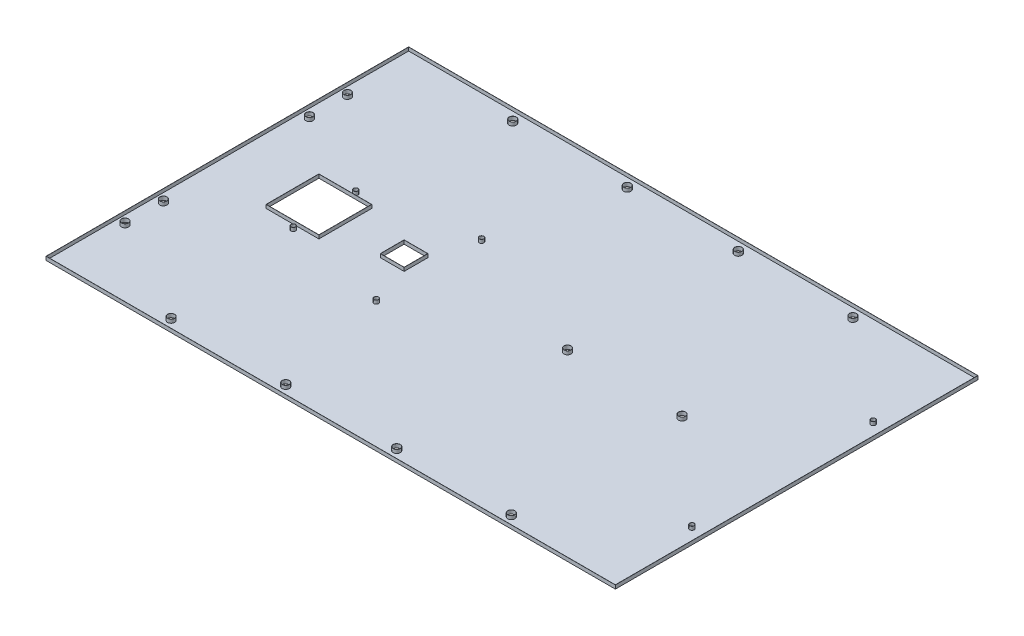
SolidWorks part; units mm, degrees
ref_plane "Front Plane" through (0, 0, 0) normal (0, 0, 1) x (1, 0, 0)
ref_plane "Top Plane" through (0, 0, 0) normal (0, 1, 0) x (1, 0, 0)
ref_plane "Right Plane" through (0, 0, 0) normal (1, 0, 0) x (0, 0, -1)
sketch "Sketch1" plane through (0, 0, 0) normal (0, 1, 0) x (1, 0, 0)
  line L0 (0, 63.5) -> (0, -63.5)
  line L1 (-199.39, 63.5) -> (199.39, 63.5)
  line L2 (-199.39, 63.5) -> (-199.39, -63.5)
  line L3 (-199.39, -63.5) -> (199.39, -63.5)
  line L4 (199.39, 63.5) -> (199.39, -63.5)
  dimension "D1" = 398.78
  dimension "D2" = 127
extrude "Boss-Extrude1" add sketch "Sketch1" along normal blind 2.54 contours L2 L3 L0 L1 | L4 L1 L0 L3
hole_wizard "#11 (0.191) Diameter Hole1" positions "Sketch6" profile "Sketch5" hole size "#11" standard "ANSI Inch" end condition through all
sketch "Sketch6" plane through (0, 2.54, 0) normal (0, 1, 0) x (1, 0, 0)
  line L0 (-199.39, 63.5) -> (-199.39, -63.5) construction
  line L1 (-199.39, -63.5) -> (199.39, -63.5) construction
  point P0 (-193.167, -14.4018)
  point P2 (-193.04, 12.3444)
  dimension "D1" = 6.223
  dimension "D2" = 49.0982
  dimension "D4" = 75.8444
sketch "Sketch5" plane through (-193.167, 2.54, 14.4018) normal (1, 0, 0) x (0, 0, 1)
  line L0 (0, 0) -> (0, 2.54)
  line L1 (0, 2.54) -> (2.4257, 2.54)
  line L2 (2.4257, 2.54) -> (2.4257, 0)
  line L5 (2.4257, 0) -> (0, 0)
  line L11 (0, -6.35) -> (0, 107.95) construction
  dimension "Thru Hole Dia." = 4.8514
  dimension "Thru Hole Depth" = 2.54
sketch "Sketch8" plane through (0, 2.54, 0) normal (0, 1, 0) x (1, 0, 0)
  line L0 (-199.39, 63.5) -> (199.39, 63.5) construction
  line L1 (-153.67, 63.5) -> (-116.84, 63.5)
  line L2 (-153.67, 63.5) -> (-153.67, 45.085)
  line L3 (-153.67, 45.085) -> (-116.84, 45.085)
  line L4 (-116.84, 63.5) -> (-116.84, 45.085)
  line L5 (-199.39, 63.5) -> (-199.39, -63.5) construction
  line L8 (-83.82, 63.5) -> (-67.31, 63.5)
  line L9 (-83.82, 63.5) -> (-83.82, 55.245)
  line L10 (-83.82, 55.245) -> (-67.31, 55.245)
  line L11 (-67.31, 63.5) -> (-67.31, 55.245)
  dimension "D1" = 18.415
  dimension "D2" = 36.83
  dimension "D3" = 45.72
  dimension "D4" = 16.51
  dimension "D5" = 8.255
  dimension "D6" = 33.02
hole_wizard "#11 (0.191) Diameter Hole2" positions "Sketch10" profile "Sketch9" hole size "#11" standard "ANSI Inch" end condition through all
sketch "Sketch10" plane through (0, 2.54, 0) normal (0, 1, 0) x (1, 0, 0)
  line L0 (-199.39, 63.5) -> (-199.39, -63.5) construction
  line L1 (199.39, 63.5) -> (199.39, -63.5) construction
  point P0 (-119.126, -56.1278)
  point P2 (-38.862, -56.1278)
  point P4 (38.862, -56.1278)
  point P6 (119.126, -56.1278)
  dimension "D1" = 80.264
  dimension "D2" = 80.264
  dimension "D3" = 80.264
  dimension "D4" = 80.264
sketch "Sketch9" plane through (-119.126, 2.54, 56.1278) normal (1, 0, 0) x (0, 0, 1)
  line L0 (0, 0) -> (0, 2.54)
  line L1 (0, 2.54) -> (2.4257, 2.54)
  line L2 (2.4257, 2.54) -> (2.4257, 0)
  line L5 (2.4257, 0) -> (0, 0)
  line L11 (0, -6.35) -> (0, 107.95) construction
  dimension "Thru Hole Dia." = 4.8514
  dimension "Thru Hole Depth" = 2.54
extrude "Cut-Extrude1" cut sketch "Sketch8" against normal blind 2.54
mirror "Mirror6" about plane through (0, 2.54, -63.5) normal (0, 0, -1) of "Cut-Extrude1", "#11 (0.191) Diameter Hole1", "#11 (0.191) Diameter Hole2", "Boss-Extrude1"
hole_wizard "#11 (0.191) Diameter Hole3" positions "Sketch14" profile "Sketch13" hole size "#11" standard "ANSI Inch" end condition through all
sketch "Sketch14" plane through (0, 2.54, 0) normal (0, 1, 0) x (1, 0, 0)
  point P0 (119.126, 63.5)
  point P2 (38.862, 63.5)
sketch "Sketch13" plane through (119.126, 2.54, -63.5) normal (1, 0, 0) x (0, 0, 1)
  line L0 (0, 0) -> (0, 2.54)
  line L1 (0, 2.54) -> (2.4257, 2.54)
  line L2 (2.4257, 2.54) -> (2.4257, 0)
  line L5 (2.4257, 0) -> (0, 0)
  line L11 (0, -6.35) -> (0, 107.95) construction
  dimension "Thru Hole Dia." = 4.8514
  dimension "Thru Hole Depth" = 2.54
hole_wizard "#31 (0.12) Diameter Hole2" positions "Sketch19" profile "Sketch18" hole size "#31" standard "ANSI Inch" end condition through all
sketch "Sketch19" plane through (0, 2.54, 0) normal (0, 1, 0) x (1, 0, 0)
  line L2 (-153.67, 81.915) -> (-116.84, 81.915) construction
  line L3 (-153.67, 45.085) -> (-116.84, 45.085) construction
  line L4 (-199.39, 190.5) -> (-199.39, -63.5) construction
  point P0 (-131.318, 41.656)
  point P2 (-131.318, 85.344)
  dimension "D1" = 43.688
  dimension "D2" = 3.429
  dimension "D3" = 3.429
  dimension "D4" = 68.072
sketch "Sketch18" plane through (-131.318, 2.54, -41.656) normal (1, 0, 0) x (0, 0, 1)
  line L0 (0, 0) -> (0, 2.54)
  line L1 (0, 2.54) -> (1.524, 2.54)
  line L2 (1.524, 2.54) -> (1.524, 0)
  line L5 (1.524, 0) -> (0, 0)
  line L11 (0, -6.35) -> (0, 107.95) construction
  dimension "Thru Hole Dia." = 3.048
  dimension "Thru Hole Depth" = 2.54
hole_wizard "#31 (0.12) Diameter Hole3" positions "Sketch21" profile "Sketch20" hole size "#31" standard "ANSI Inch" end condition through all
sketch "Sketch21" plane through (0, 2.54, 0) normal (0, 1, 0) x (1, 0, 0)
  line L0 (-199.39, 190.5) -> (-199.39, -63.5) construction
  line L2 (-83.82, 71.755) -> (-67.31, 71.755) construction
  point P0 (-58.166, 100.33)
  point P2 (-58.166, 26.67)
  dimension "D1" = 141.224
  dimension "D2" = 73.66
  dimension "D3" = 28.575
sketch "Sketch20" plane through (-58.166, 2.54, -100.33) normal (1, 0, 0) x (0, 0, 1)
  line L0 (0, 0) -> (0, 2.54)
  line L1 (0, 2.54) -> (1.524, 2.54)
  line L2 (1.524, 2.54) -> (1.524, 0)
  line L5 (1.524, 0) -> (0, 0)
  line L11 (0, -6.35) -> (0, 107.95) construction
  dimension "Thru Hole Dia." = 3.048
  dimension "Thru Hole Depth" = 2.54
hole_wizard "1/8 (0.125) Diameter Hole1" positions "Sketch23" profile "Sketch22" hole size "1/8" standard "ANSI Inch" end condition through all
sketch "Sketch23" plane through (0, 2.54, 0) normal (0, 1, 0) x (1, 0, 0)
  line L0 (-199.39, -63.5) -> (199.39, -63.5) construction
  line L1 (-199.39, 190.5) -> (199.39, 190.5) construction
  line L2 (199.39, 190.5) -> (199.39, -63.5) construction
  point P0 (189.484, 0)
  point P2 (189.484, 127)
  dimension "D1" = 63.5
  dimension "D2" = 63.5
  dimension "D3" = 9.906
sketch "Sketch22" plane through (189.484, 2.54, 0) normal (1, 0, 0) x (0, 0, 1)
  line L0 (0, 0) -> (0, 2.54)
  line L1 (0, 2.54) -> (1.524, 2.54)
  line L2 (1.524, 2.54) -> (1.524, 0)
  line L5 (1.524, 0) -> (0, 0)
  line L11 (0, -6.35) -> (0, 107.95) construction
  dimension "Thru Hole Dia." = 3.048
  dimension "Thru Hole Depth" = 2.54
shell "Shell1" thickness 0.1016
